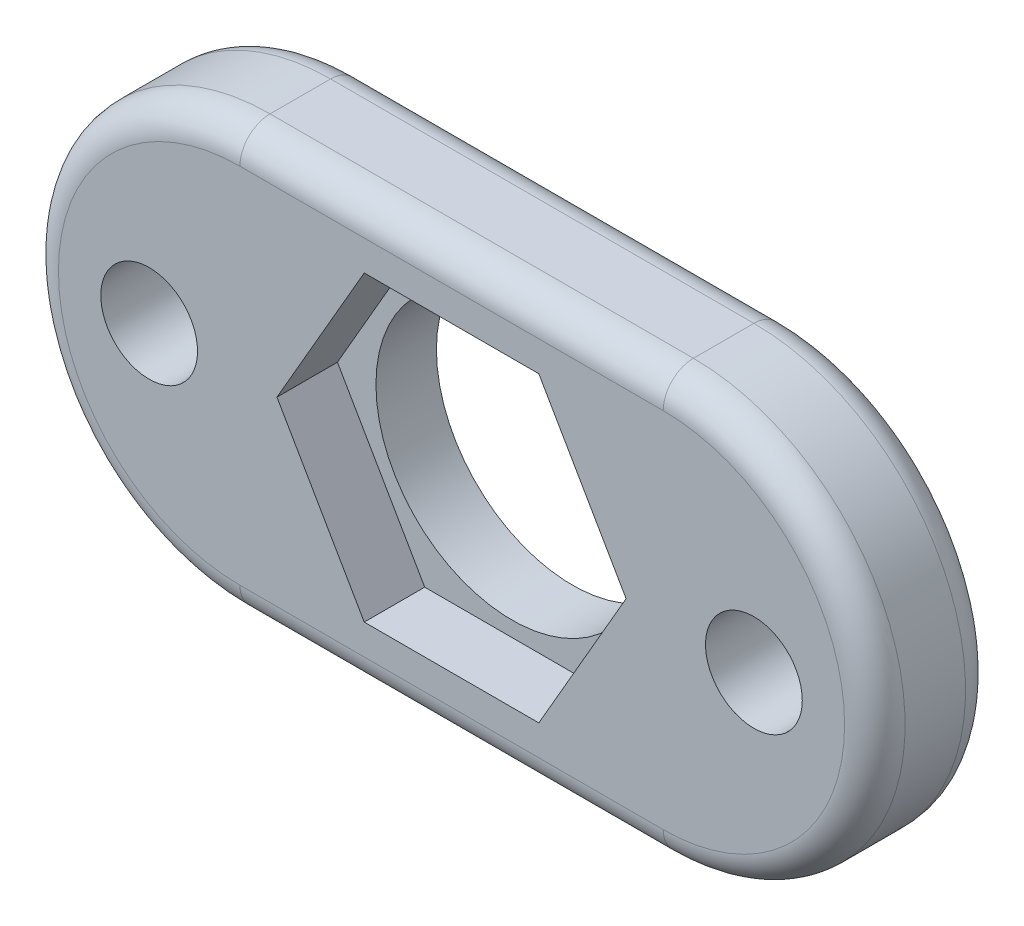
SolidWorks part; units mm, degrees
ref_plane "Plan de face" through (0, 0, 0) normal (0, 0, 1) x (1, 0, 0)
ref_plane "Plan de dessus" through (0, 0, 0) normal (0, 1, 0) x (1, 0, 0)
ref_plane "Plan de droite" through (0, 0, 0) normal (1, 0, 0) x (0, 0, -1)
sketch "Esquisse1" plane through (0, 0, 0) normal (0, 0, 1) x (1, 0, 0)
  line L0 (-27.2542, 0) -> (-13.2542, 0) construction
  line L1 (-27.2542, 7) -> (-13.2542, 7)
  line L2 (-27.2542, -7) -> (-13.2542, -7)
  arc A0 (-27.2542, 7) -> (-27.2542, -7) centre (-27.2542, 0) ccw
  arc A1 (-13.2542, -7) -> (-13.2542, 7) centre (-13.2542, 0) ccw
  point P3 (-20.2542, 0)
  dimension "D1" = 14
  dimension "D2" = 14
extrude "Boss.-Extru.1" add sketch "Esquisse1" along normal blind 4
sketch "Esquisse3" plane through (0, 0, 4) normal (0, 0, 1) x (1, 0, 0)
  line L0 (-27.2542, -7) -> (-13.2542, -7) construction
  circle A0 centre (-20.2542, 0) radius 4.5
  circle A1 centre (-30.2542, 0) radius 1.6
  circle A2 centre (-10.2542, 0) radius 1.6
  dimension "D1" = 3.2
  dimension "D2" = 3.2
  dimension "D5" = 9
  dimension "D3" = 20
  dimension "D4" = 10
  dimension "D6" = 7
  dimension "D7" = 7
  dimension "D8" = 7
  dimension "D9" = 7
extrude "Enlèv. mat.-Extru.1" cut sketch "Esquisse3" against normal through all
sketch "Esquisse4" plane through (0, 0, 4) normal (0, 0, 1) x (1, 0, 0)
  line L0 (-13.2542, 7) -> (-27.2542, 7) construction
  line L1 (-23.1409, 5) -> (-26.0277, 0)
  line L2 (-26.0277, 0) -> (-23.1409, -5)
  line L3 (-23.1409, -5) -> (-17.3674, -5)
  line L4 (-17.3674, -5) -> (-14.4807, 0)
  line L5 (-14.4807, 0) -> (-17.3674, 5)
  line L6 (-17.3674, 5) -> (-23.1409, 5)
  circle A0 centre (-20.2542, 0) radius 5 construction
  dimension "D1" = 10
extrude "Enlèv. mat.-Extru.2" cut sketch "Esquisse4" against normal blind 2
fillet "Congé1" radius 1 8 edges at (-20.2542, 7, 4) (-6.2542, 0, 4) (-20.2542, -7, 4) (-20.2542, 7, 0) (-6.2542, 0, 0) (-20.2542, -7, 0) (-34.2542, 0, 4) (-34.2542, 0, 0)
